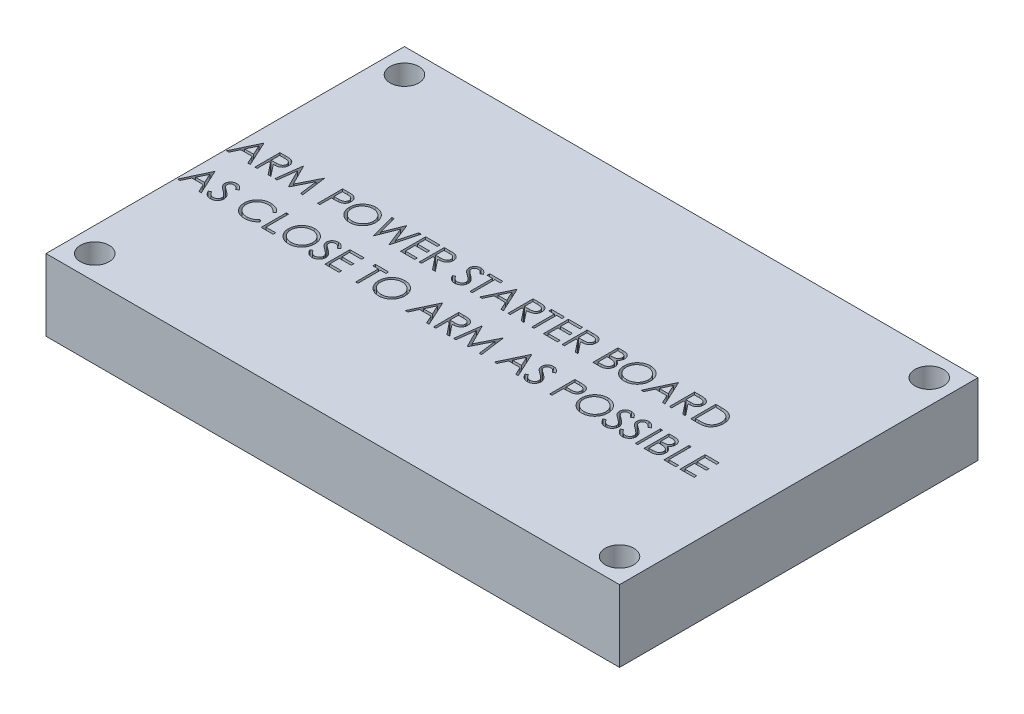
SolidWorks part; units mm, degrees
ref_plane "Front Plane" through (0, 0, 0) normal (0, 0, 1) x (1, 0, 0)
ref_plane "Top Plane" through (0, 0, 0) normal (0, 1, 0) x (1, 0, 0)
ref_plane "Right Plane" through (0, 0, 0) normal (1, 0, 0) x (0, 0, -1)
sketch "Sketch1" plane through (0, 0, 0) normal (0, 1, 0) x (1, 0, 0)
  line L1 (0, 0) -> (80, 0)
  line L2 (0, 0) -> (0, 50)
  line L3 (0, 50) -> (80, 50)
  line L4 (80, 0) -> (80, 50)
  circle A0 centre (3.4, 46.6) radius 2
  circle A1 centre (3.4, 3.4) radius 2
  circle A2 centre (76.6, 46.6) radius 2
  circle A3 centre (76.6, 3.4) radius 2
  point P13 (0, 0)
  point P14 (0, 0)
  point P15 (0, 3.9314)
  point P16 (0, 0)
  dimension "D3" = 3.4
  dimension "D4" = 3.4
  dimension "D5" = 3.4
  dimension "D6" = 3.4
  dimension "D9" = 3.4
  dimension "D1" = 50
  dimension "D2" = 80
  dimension "D7" = 3.4
  dimension "D8" = 3.4
  dimension "D10" = 3.4
extrude "Boss-Extrude1" add sketch "Sketch1" along normal blind 10
sketch "Sketch2" plane through (0, 10, 0) normal (0, 1, 0) x (1, 0, 0)
  line L0 (0, 25) -> (80, 25) construction
  line L1 (0, 50) -> (0, 0) construction
  line L2 (80, 0) -> (80, 50) construction
  text T0 "ARM POWER STARTER BOARD\r\nAS CLOSE TO ARM AS POSSIBLE"
extrude "Cut-Extrude1" cut sketch "Sketch2" against normal through all
